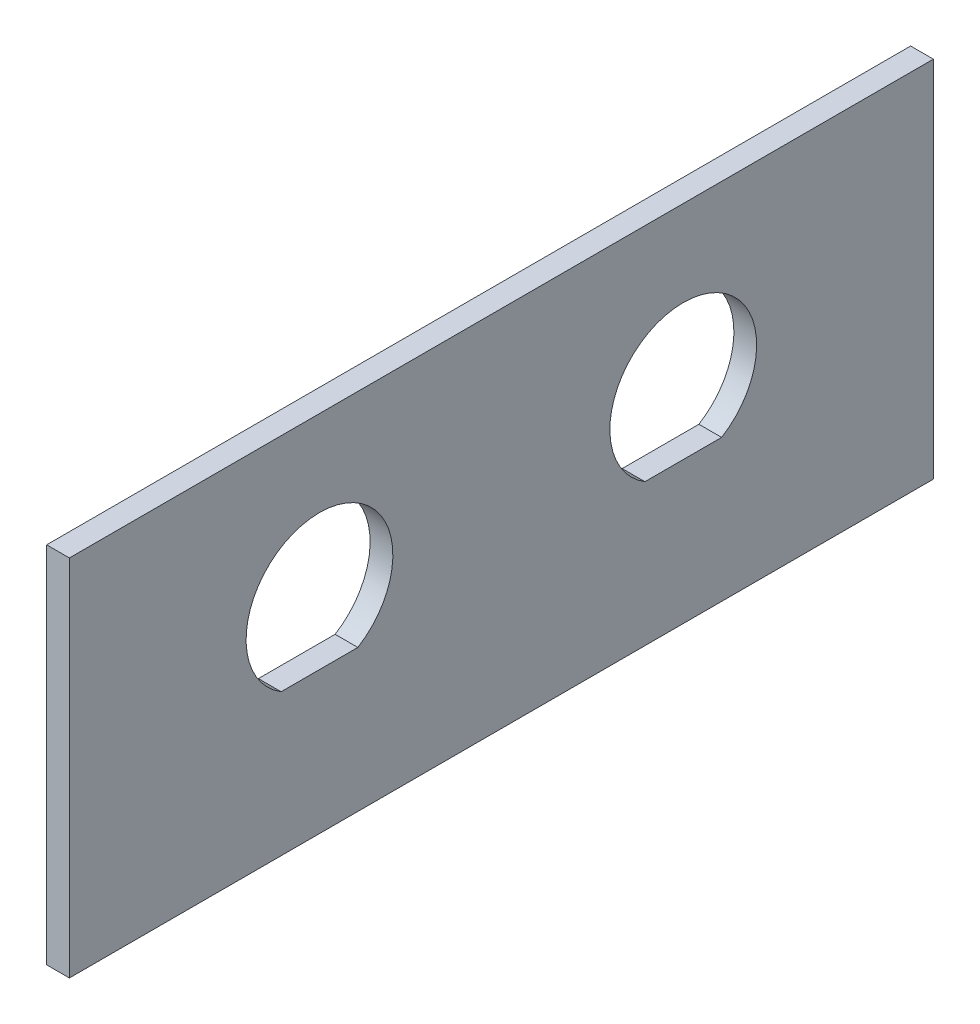
SolidWorks part; units mm, degrees
material "6061-T6 (SS)"
ref_plane "Front Plane" through (0, 0, 0) normal (0, 0, 1) x (1, 0, 0)
ref_plane "Top Plane" through (0, 0, 0) normal (0, 1, 0) x (1, 0, 0)
ref_plane "Right Plane" through (0, 0, 0) normal (1, 0, 0) x (0, 0, -1)
sketch "Sketch1" plane through (0, 0, 0) normal (0, 1, 0) x (1, 0, 0)
  line L1 (101.6, -60.325) -> (-101.6, -60.325)
  line L2 (101.6, -60.325) -> (101.6, 60.325)
  line L3 (101.6, 60.325) -> (-101.6, 60.325)
  line L4 (-101.6, -60.325) -> (-101.6, 60.325)
  line L5 (101.6, -60.325) -> (-101.6, 60.325) construction
  line L6 (101.6, 60.325) -> (-101.6, -60.325) construction
  point P0 (0, 0)
  dimension "D1" = 120.65
  dimension "D2" = 203.2
extrude "Boss-Extrude1" add sketch "Sketch1" along normal blind 50.8
sketch "Sketch2" plane through (0, 50.8, 0) normal (0, 1, 0) x (1, 0, 0)
  line L8 (-98.425, 57.15) -> (-98.425, -57.15)
  line L9 (98.425, 57.15) -> (-98.425, 57.15)
  line L10 (98.425, -57.15) -> (98.425, 57.15)
  line L11 (-98.425, -57.15) -> (98.425, -57.15)
  line L12 (-98.425, 57.15) -> (-98.425, -57.15)
  line L13 (98.425, 57.15) -> (-98.425, 57.15)
  line L14 (98.425, -57.15) -> (98.425, 57.15)
  line L15 (-98.425, -57.15) -> (98.425, -57.15)
  dimension "D1" = 3.175
extrude "Cut-Extrude1" cut sketch "Sketch2" against normal through all
sketch "Sketch4" plane through (0, 50.8, 0) normal (0, 1, 0) x (1, 0, 0)
  line L4 (101.6, 60.325) -> (-101.6, 60.325)
  line L5 (-101.6, 60.325) -> (-101.6, -60.325)
  line L6 (-101.6, -60.325) -> (101.6, -60.325)
  line L7 (101.6, -60.325) -> (101.6, 60.325)
  line L9 (-98.425, -57.15) -> (98.425, -57.15)
  line L10 (-98.425, -57.15) -> (-98.425, 57.15)
  line L11 (-98.425, 57.15) -> (98.425, 57.15)
  line L12 (98.425, -57.15) -> (98.425, 57.15)
  line L13 (-98.425, -57.15) -> (98.425, 57.15) construction
  line L14 (-98.425, 57.15) -> (98.425, -57.15) construction
  point P12 (0, 0)
  dimension "D1" = 3.175
  dimension "D2" = 3.175
  dimension "D3" = 3.175
  dimension "D4" = 3.175
extrude "Boss-Extrude2" add sketch "Sketch4" against normal blind 6.35
sketch "Sketch10" plane through (0, 0, 60.325) normal (0, 0, 1) x (1, 0, 0)
  line L0 (0, 22.225) -> (50.8, 22.225) construction
  line L1 (-101.6, 0) -> (101.6, 0) construction
  line L3 (-104.775, 13.4874) -> (104.775, 13.4874)
  line L6 (50.8, 22.225) -> (101.6, 22.225) construction
  line L7 (101.6, 50.8) -> (101.6, 0) construction
  line L8 (0, 22.225) -> (-50.8, 22.225) construction
  line L9 (-50.8, 22.225) -> (-101.6, 22.225) construction
  line L10 (-101.6, 50.8) -> (-101.6, 0) construction
  circle A0 centre (-76.2, 22.225) radius 10.2489
  circle A1 centre (-25.4, 22.225) radius 10.2489
  circle A2 centre (25.4, 22.225) radius 10.2489
  circle A3 centre (76.2, 22.225) radius 10.2489
  point P5 (-76.2, 22.225)
  point P9 (-25.4, 22.225)
  point P12 (25.4, 22.225)
  point P13 (76.2, 22.225)
  dimension "D2" = 22.225
  dimension "D1" = 20.4978
  dimension "D3" = 8.7376
extrude "Cut-Extrude5" cut sketch "Sketch10" against normal through all
sketch "Sketch12" plane through (101.6, 0, 0) normal (1, 0, 0) x (0, 0, -1)
  line L0 (60.325, 28.575) -> (-60.325, 28.575) construction
  line L1 (60.325, 50.8) -> (60.325, 0) construction
  line L2 (-60.325, 50.8) -> (-60.325, 0) construction
  line L3 (-60.325, 0) -> (60.325, 0) construction
  line L4 (-60.325, 19.8374) -> (60.325, 19.8374)
  circle A0 centre (-25.4, 28.575) radius 10.2489
  circle A1 centre (25.4, 28.575) radius 10.2489
  point P6 (60.325, 28.575)
  point P7 (-25.4, 28.575)
  point P10 (25.4, 28.575)
  dimension "D2" = 8.7376
  dimension "D3" = 20.4978
  dimension "D5" = 28.575
  dimension "D1" = 34.925
  dimension "D4" = 34.925
extrude "Cut-Extrude6" cut sketch "Sketch12" against normal up to next
sketch "Sketch13" plane through (-101.6, 0, 0) normal (-1, 0, 0) x (0, 0, 1)
  line L0 (60.325, 25.4) -> (-60.325, 25.4) construction
  line L1 (60.325, 50.8) -> (60.325, 0) construction
  line L2 (-60.325, 50.8) -> (-60.325, 0) construction
  line L4 (-60.325, 50.8) -> (60.325, 50.8) construction
  circle A0 centre (15.875, 28.575) radius 12.554
  point P6 (22.225, 25.4)
  point P7 (15.875, 28.575)
  dimension "D3" = 25.1079
  dimension "D4" = 22.225
  dimension "D1" = 38.1
  dimension "D2" = 76.2
extrude "Cut-Extrude7" cut sketch "Sketch13" against normal up to next
sketch "Sketch14" plane through (0, 50.8, 0) normal (0, 1, 0) x (1, 0, 0)
  line L0 (101.6, 60.325) -> (-101.6, 60.325) construction
  line L2 (98.425, 60.325) -> (-101.6, 60.325)
  line L3 (98.425, 60.325) -> (98.425, -60.325)
  line L4 (98.425, -60.325) -> (-101.6, -60.325)
  line L6 (-101.6, 60.325) -> (-101.6, -60.325)
  line L7 (101.6, -60.325) -> (101.6, 60.325) construction
  dimension "D1" = 3.175
extrude "Cut-Extrude8" cut sketch "Sketch14" against normal through all
